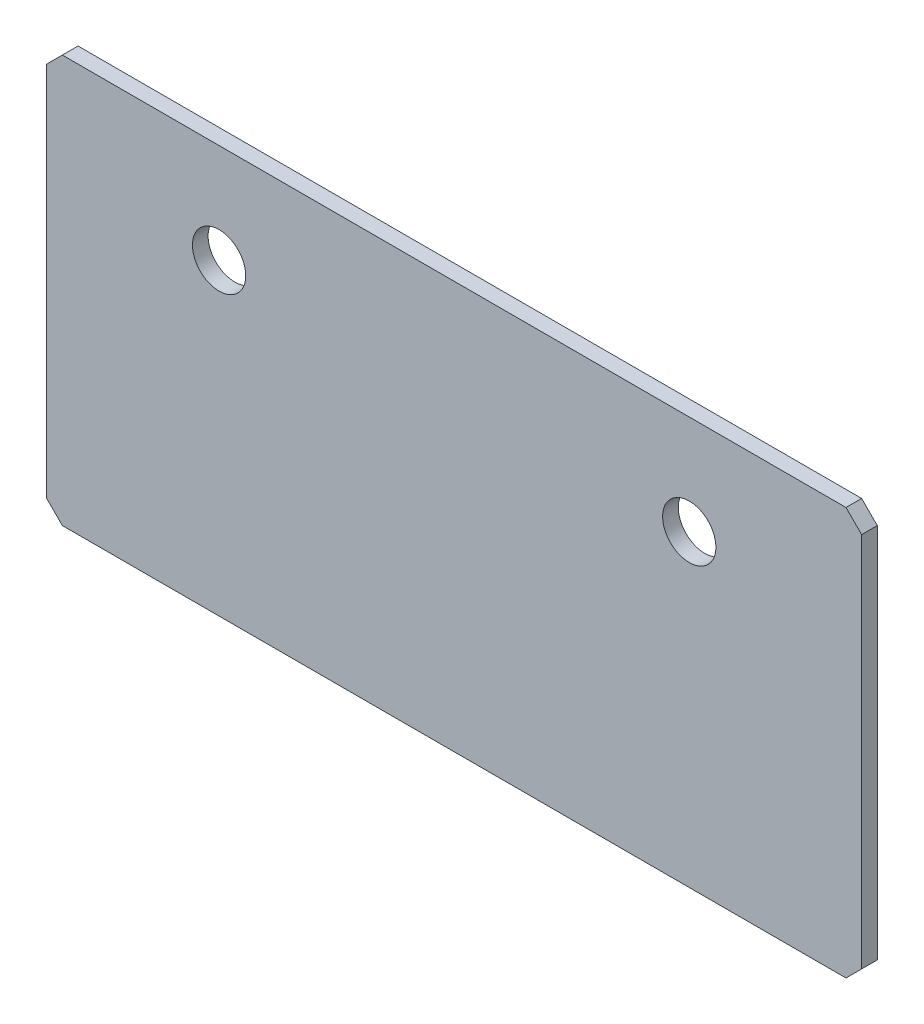
SolidWorks part; units mm, degrees
ref_plane "Front Plane" through (0, 0, 0) normal (0, 0, 1) x (1, 0, 0)
ref_plane "Top Plane" through (0, 0, 0) normal (0, 1, 0) x (1, 0, 0)
ref_plane "Right Plane" through (0, 0, 0) normal (1, 0, 0) x (0, 0, -1)
sketch "Sketch1" plane through (0, 0, 0) normal (0, 0, 1) x (1, 0, 0)
  line L1 (0, 0) -> (52, 0)
  line L2 (0, 0) -> (0, -26)
  line L3 (0, -26) -> (52, -26)
  line L4 (52, 0) -> (52, -26)
  circle A0 centre (11, -6.344) radius 1.7
  circle A1 centre (41, -6.344) radius 1.7
  point P9 (0, 0)
  dimension "D3" = 3.4
  dimension "D1" = 52
  dimension "D2" = 26
  dimension "D4" = 11
  dimension "D5" = 30
extrude "Boss-Extrude1" add sketch "Sketch1" along normal blind 1
chamfer "Chamfer1" distance 1 angle 45 4 edges at (52, 0, 0.5) (52, -26, 0.5) (0, -26, 0.5) (0, 0, 0.5)
